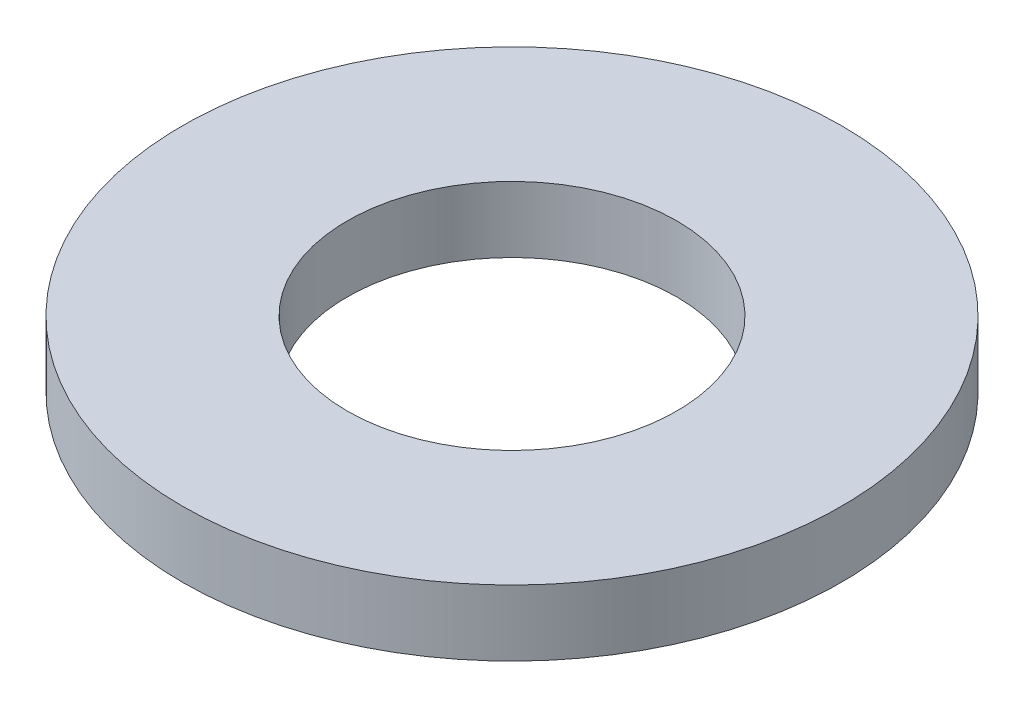
SolidWorks part; units mm, degrees
material "AISI 304"
ref_plane "Front Plane" through (0, 0, 0) normal (0, 0, 1) x (1, 0, 0)
ref_plane "Top Plane" through (0, 0, 0) normal (0, 1, 0) x (1, 0, 0)
ref_plane "Right Plane" through (0, 0, 0) normal (1, 0, 0) x (0, 0, -1)
sketch "Sketch1" plane through (0, 0, 0) normal (0, 1, 0) x (1, 0, 0)
  circle A0 centre (0, 0) radius 5
  circle A1 centre (0, 0) radius 2.5
  dimension "D1" = 5
  dimension "D2" = 10
extrude "Boss-Extrude1" add sketch "Sketch1" along normal blind 1
